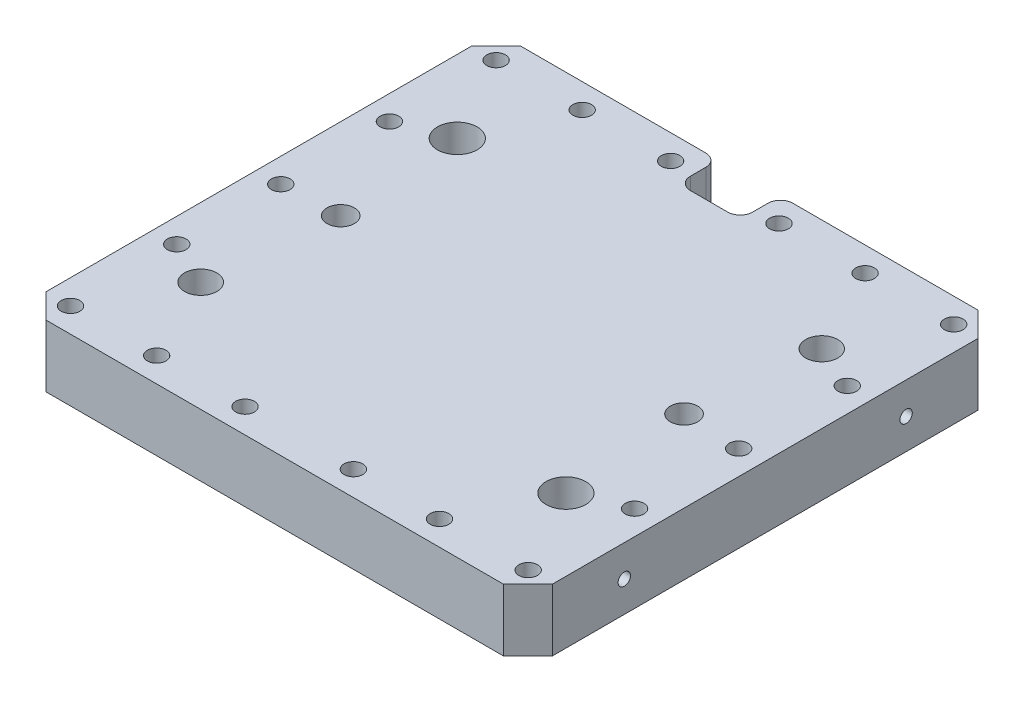
SolidWorks part; units mm, degrees
ref_plane "Front Plane" through (0, 0, 0) normal (0, 0, 1) x (1, 0, 0)
ref_plane "Top Plane" through (0, 0, 0) normal (0, 1, 0) x (1, 0, 0)
ref_plane "Right Plane" through (0, 0, 0) normal (1, 0, 0) x (0, 0, -1)
sketch "Sketch1" plane through (0, 0, 0) normal (0, 1, 0) x (1, 0, 0)
  line L0 (-116.078, -5.08) -> (-116.078, -11.3538)
  line L1 (-10, 0) -> (-85.598, 0)
  line L2 (0, -10) -> (0, -183.7766)
  line L3 (-10, -193.7766) -> (-196.756, -193.7766)
  line L4 (-206.756, -10) -> (-206.756, -183.7766)
  line L5 (-110.998, -16.4338) -> (-95.758, -16.4338)
  line L6 (-90.678, -11.3538) -> (-90.678, -5.08)
  line L7 (-121.158, 0) -> (-196.756, 0)
  line L8 (-196.756, 0) -> (-206.756, -10)
  line L9 (0, -10) -> (-10, 0)
  line L10 (0, -183.7766) -> (-10, -193.7766)
  line L11 (-196.756, -193.7766) -> (-206.756, -183.7766)
  arc A0 (-116.078, -11.3538) -> (-110.998, -16.4338) centre (-110.998, -11.3538) ccw
  arc A1 (-95.758, -16.4338) -> (-90.678, -11.3538) centre (-95.758, -11.3538) ccw
  arc A2 (-90.678, -5.08) -> (-85.598, 0) centre (-85.598, -5.08) cw
  arc A3 (-116.078, -5.08) -> (-121.158, 0) centre (-121.158, -5.08) ccw
  point P0 (0, 0)
  point P1 (-206.756, -193.7766)
  point P2 (0, -193.7766)
  point P3 (-206.756, 0)
  point P18 (-116.078, 0)
  dimension "D5" = 5.08
  dimension "D1" = 206.756
  dimension "D2" = 193.7766
  dimension "D3" = 25.4
  dimension "D4" = 16.4338
  dimension "D6" = 90.678
extrude "Boss-Extrude1" add sketch "Sketch1" along normal mid plane 25.4
sketch "Sketch4" plane through (0, 0, 0) normal (1, 0, 0) x (0, 0, -1)
  line L0 (-96.8883, 12.7) -> (-96.8883, -12.7) construction
  line L1 (-39.3573, -2.7305) -> (-37.5506, -2.7305) construction
  line L2 (-183.7766, -12.7) -> (-10, -12.7) construction
  line L3 (-36.83, -0.2032) -> (-36.83, 7.988) construction
  line L4 (0, 12.7) -> (0, -12.7) construction
  line L5 (-183.7766, 12.7) -> (-10, 12.7) construction
  circle A0 centre (-39.3573, -0.2032) radius 2.5273
  circle A1 centre (-154.4193, -0.2032) radius 2.5273
  dimension "D2" = 5.0546
  dimension "D1" = 9.9695
  dimension "D3" = 36.83
extrude "Cut-Extrude1" cut sketch "Sketch4" against normal blind 13.5636
ref_plane "Plane2" through (-103.378, 0, 0) normal (1, 0, 0) x (0, 0, -1)
mirror "Mirror1" about plane through (-103.378, 0, 0) normal (1, 0, 0) of "Cut-Extrude1"
sketch "Sketch5" plane through (0, 12.7, 0) normal (0, 1, 0) x (1, 0, 0)
  line L0 (-200.5584, -183.769) -> (-200.5584, -167.543)
  line L1 (-206.756, -10) -> (-206.756, -183.7766) construction
  line L2 (-196.7484, -187.579) -> (-183.6304, -187.579)
  line L3 (-196.756, -193.7766) -> (-10, -193.7766) construction
  line L4 (-192.9384, -183.769) -> (-192.9384, -176.358)
  line L5 (-165.4048, -183.769) -> (-165.4048, -174.6438)
  line L6 (-157.7848, -183.769) -> (-157.7848, -174.6438)
  line L7 (-129.3114, -183.769) -> (-129.3114, -174.6438)
  line L8 (-121.6914, -183.769) -> (-121.6914, -174.6438)
  line L9 (-103.378, -242.1598) -> (-103.378, -145.3934) construction
  line L10 (-85.0646, -183.769) -> (-85.0646, -174.6438)
  line L11 (-77.4446, -183.769) -> (-77.4446, -174.6438)
  line L12 (-49.911, -183.769) -> (-49.911, -174.6438)
  line L13 (-13.716, -183.769) -> (-13.716, -178.3031)
  line L14 (-42.291, -183.769) -> (-42.291, -178.3752)
  line L15 (-6.096, -183.769) -> (-6.096, -177.7114)
  line L16 (0, -183.7766) -> (0, -10) construction
  line L17 (-9.906, -187.579) -> (-13.716, -187.579)
  line L18 (-264.7683, -96.8883) -> (83.4452, -96.8883) construction
  line L19 (-9.906, -6.1976) -> (-13.716, -6.1976)
  line L20 (-6.096, -10.0076) -> (-6.096, -16.0652)
  line L21 (-42.291, -10.0076) -> (-42.291, -15.4014)
  line L22 (-13.716, -10.0076) -> (-13.716, -15.4735)
  line L23 (-49.911, -10.0076) -> (-49.911, -19.1328)
  line L24 (-77.4446, -10.0076) -> (-77.4446, -19.1328)
  line L25 (-85.0646, -10.0076) -> (-85.0646, -19.1328)
  line L26 (-121.6914, -10.0076) -> (-121.6914, -19.1328)
  line L27 (-129.3114, -10.0076) -> (-129.3114, -19.1328)
  line L28 (-157.7848, -10.0076) -> (-157.7848, -19.1328)
  line L29 (-165.4048, -10.0076) -> (-165.4048, -19.1328)
  line L30 (-192.9384, -10.0076) -> (-192.9384, -17.4186)
  line L31 (-196.7484, -6.1976) -> (-183.6304, -6.1976)
  line L32 (-200.5584, -10.0076) -> (-200.5584, -26.2336)
  line L33 (-103.378, -16.4338) -> (-103.378, -193.7766) construction
  line L34 (-95.758, -16.4338) -> (-110.998, -16.4338) construction
  line L35 (-9.906, -57.277) -> (-4.2227, -57.277)
  line L36 (-9.906, -94.0054) -> (-17.375, -94.0054)
  line L37 (-9.906, -136.4996) -> (-14.922, -136.4996)
  line L38 (-9.906, -101.6254) -> (-15.9916, -101.6254)
  circle A0 centre (-196.7484, -183.769) radius 3.81
  circle A1 centre (-161.5948, -183.769) radius 3.81
  circle A2 centre (-125.5014, -183.769) radius 3.81
  circle A3 centre (-81.2546, -183.769) radius 3.81
  circle A4 centre (-46.101, -183.769) radius 3.81
  circle A5 centre (-9.906, -183.769) radius 3.81
  circle A6 centre (-9.906, -10.0076) radius 3.81
  circle A7 centre (-46.101, -10.0076) radius 3.81
  circle A8 centre (-81.2546, -10.0076) radius 3.81
  circle A9 centre (-125.5014, -10.0076) radius 3.81
  circle A10 centre (-161.5948, -10.0076) radius 3.81
  circle A11 centre (-196.7484, -10.0076) radius 3.81
  circle A12 centre (-9.906, -53.467) radius 3.81
  circle A13 centre (-9.906, -97.8154) radius 3.81
  circle A14 centre (-9.906, -140.3096) radius 3.81
  circle A15 centre (-196.85, -140.3096) radius 3.81
  circle A16 centre (-196.85, -97.8154) radius 3.81
  circle A17 centre (-196.85, -53.467) radius 3.81
  point P44 (-103.378, -193.7766)
  point P45 (-103.378, -193.7766)
  point P52 (0, -96.8883)
  dimension "D2" = 7.62
  dimension "D14" = 7.62
  dimension "D15" = 7.62
  dimension "D13" = 7.62
  dimension "D1" = 6.1976
  dimension "D3" = 6.1976
  dimension "D4" = 42.7736
  dimension "D5" = 25.9334
  dimension "D6" = 25.9334
  dimension "D7" = 42.7736
  dimension "D8" = 6.096
  dimension "D9" = 6.1976
  dimension "D10" = 51.0794
  dimension "D11" = 36.7284
  dimension "D12" = 51.0794
extrude "Cut-Extrude2" cut sketch "Sketch5" against normal through all both and the other way through all contours A11 | A10 | A9 | A8 | A5 | A4 | A3 | A2 | A1 | A0 | A12 | A13 | A14 | A17 | A16 | A15 | A7 | A6
sketch "Sketch6" plane through (0, 12.7, 0) normal (0, 1, 0) x (1, 0, 0)
  line L0 (-103.378, -16.4338) -> (-103.378, -193.7766) construction
  line L1 (-95.758, -16.4338) -> (-110.998, -16.4338) construction
  line L2 (-196.756, -193.7766) -> (-10, -193.7766) construction
  line L3 (-28.2321, -39.0144) -> (-62.5548, -39.0144)
  line L4 (-10, 0) -> (-85.598, 0) construction
  line L5 (-21.6789, -45.5676) -> (-21.6789, -65.2219)
  line L6 (0, -183.7766) -> (0, -10) construction
  line L7 (-27.7114, -96.7232) -> (-27.7114, -112.2132)
  line L8 (-21.3106, -148.8186) -> (-21.3106, -134.9624)
  line L9 (-29.4386, -156.9466) -> (-15.0732, -156.9466)
  line L10 (-185.166, -45.5676) -> (-185.166, -56.0757)
  line L11 (-206.756, -10) -> (-206.756, -183.7766) construction
  line L12 (-33.2994, -102.3112) -> (-73.7512, -102.3112)
  line L13 (-179.07, -96.7232) -> (-179.07, -84.1428)
  line L14 (-178.562, -155.4226) -> (-185.166, -155.4226)
  line L15 (-185.166, -148.8186) -> (-185.166, -144.0496)
  circle A0 centre (-28.2321, -45.5676) radius 6.5532
  circle A1 centre (-33.2994, -96.7232) radius 5.588
  circle A2 centre (-29.4386, -148.8186) radius 8.128
  circle A3 centre (-177.038, -45.5676) radius 8.128
  circle A4 centre (-173.482, -96.7232) radius 5.588
  circle A5 centre (-178.562, -148.8186) radius 6.604
  dimension "D4" = 13.1064
  dimension "D5" = 11.176
  dimension "D8" = 16.256
  dimension "D9" = 16.256
  dimension "D10" = 11.176
  dimension "D11" = 13.208
  dimension "D1" = 39.0144
  dimension "D2" = 21.6789
  dimension "D3" = 27.7114
  dimension "D6" = 21.3106
  dimension "D7" = 36.83
  dimension "D12" = 21.59
  dimension "D13" = 91.4654
  dimension "D14" = 27.686
  dimension "D15" = 21.59
extrude "Cut-Extrude3" cut sketch "Sketch6" against normal blind 12.7 contours A3 | A4 | A5 | A0 | A1 | A2
sketch "Sketch7" plane through (0, -12.7, 0) normal (0, -1, 0) x (1, 0, 0)
  line L0 (-103.378, 16.4338) -> (-103.378, 193.7766) construction
  line L1 (-95.758, 16.4338) -> (-110.998, 16.4338) construction
  line L2 (-196.756, 193.7766) -> (-10, 193.7766) construction
  line L3 (-9.6266, 119.0244) -> (-9.6266, 125.4911)
  line L4 (-28.702, 34.2138) -> (-33.4772, 34.2138)
  line L5 (-28.702, 34.2138) -> (-28.702, 72.7202)
  line L6 (-28.702, 72.7202) -> (-33.4772, 72.7202)
  line L7 (-33.4772, 34.2138) -> (-33.4772, 72.7202)
  line L12 (0, 183.7766) -> (0, 10) construction
  line L13 (-28.0314, 88.6079) -> (-35.9054, 88.6079)
  line L14 (-28.0314, 88.6079) -> (-28.0314, 107.0229)
  line L15 (-28.0314, 107.0229) -> (-35.9054, 107.0229)
  line L16 (-35.9054, 88.6079) -> (-35.9054, 107.0229)
  line L17 (-9.6266, 74.7522) -> (-9.6266, 71.1306)
  line L18 (-28.702, 121.0056) -> (-33.528, 121.0056)
  line L19 (-28.702, 121.0056) -> (-28.702, 159.6136)
  line L20 (-28.702, 159.6136) -> (-33.528, 159.6136)
  line L21 (-33.528, 121.0056) -> (-33.528, 159.6136)
  line L22 (-15.2146, 80.3402) -> (-9.6266, 80.3402)
  line L23 (-15.2146, 113.4364) -> (-13.0826, 113.4364)
  line L24 (-191.5414, 113.4364) -> (-193.6734, 113.4364)
  line L25 (-191.5414, 80.3402) -> (-197.1294, 80.3402)
  line L26 (-173.228, 121.0056) -> (-173.228, 159.6136)
  line L27 (-178.054, 159.6136) -> (-173.228, 159.6136)
  line L28 (-178.054, 121.0056) -> (-178.054, 159.6136)
  line L29 (-178.054, 121.0056) -> (-173.228, 121.0056)
  line L30 (-197.1294, 74.7522) -> (-197.1294, 71.1306)
  line L31 (-170.8506, 88.6079) -> (-170.8506, 107.0229)
  line L32 (-178.7246, 107.0229) -> (-170.8506, 107.0229)
  line L33 (-178.7246, 88.6079) -> (-178.7246, 107.0229)
  line L34 (-178.7246, 88.6079) -> (-170.8506, 88.6079)
  line L35 (-173.2788, 34.2138) -> (-173.2788, 72.7202)
  line L36 (-178.054, 72.7202) -> (-173.2788, 72.7202)
  line L37 (-178.054, 34.2138) -> (-178.054, 72.7202)
  line L38 (-178.054, 34.2138) -> (-173.2788, 34.2138)
  line L39 (-197.1294, 119.0244) -> (-197.1294, 125.4911)
  circle A1 centre (-15.2146, 119.0244) radius 5.588
  circle A2 centre (-15.2146, 74.7522) radius 5.588
  circle A3 centre (-191.5414, 74.7522) radius 5.588
  circle A4 centre (-191.5414, 119.0244) radius 5.588
  point P20 (-9.906, 140.3096)
  point P21 (-28.702, 140.3096)
  point P23 (-28.702, 53.467)
  point P24 (-9.906, 97.8154)
  point P25 (-28.0314, 97.8154)
  point P29 (-9.906, 53.467)
  point P38 (0, 96.8883)
  point P66 (-196.85, 53.467)
  point P67 (-196.85, 97.8154)
  point P68 (-196.85, 140.3096)
  dimension "D13" = 11.176
  dimension "D14" = 11.176
  dimension "D1" = 4.7752
  dimension "D2" = 38.608
  dimension "D3" = 38.5064
  dimension "D4" = 4.826
  dimension "D5" = 69.9008
  dimension "D6" = 69.85
  dimension "D7" = 28.0314
  dimension "D8" = 7.874
  dimension "D9" = 18.415
  dimension "D10" = 9.6266
  dimension "D11" = 16.5481
  dimension "D12" = 16.5481
  dimension "D15" = 9.6266
extrude "Cut-Extrude4" cut sketch "Sketch7" against normal blind 12.7 contours L37 L38 L35 L36 | L33 L34 L31 L32 | L28 L29 L26 L27 | L21 L18 L19 L20 | L5 L6 L7 L4 | L16 L15 L14 L13
sketch "Sketch8" plane through (0, -12.7, 0) normal (0, -1, 0) x (1, 0, 0)
  circle A0 centre (-191.5414, 119.0244) radius 5.588
  circle A1 centre (-191.5414, 74.7522) radius 5.588
  circle A2 centre (-15.2146, 119.0244) radius 5.588
  circle A3 centre (-15.2146, 74.7522) radius 5.588
extrude "Cut-Extrude5" cut sketch "Sketch8" against normal blind 6.35 contours A0 | A1 | A3 | A2
